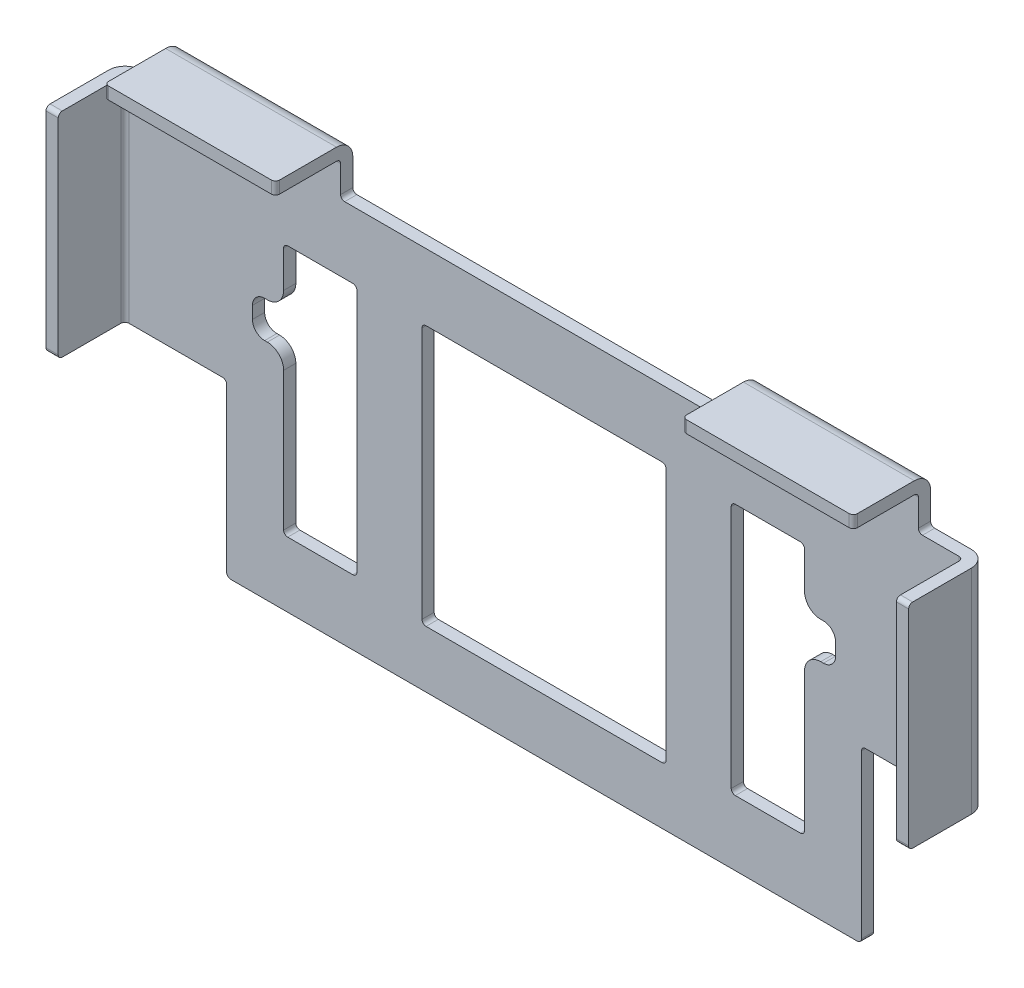
SolidWorks part; units mm, degrees
ref_plane "Front Plane" through (0, 0, 0) normal (0, 0, 1) x (1, 0, 0)
ref_plane "Top Plane" through (0, 0, 0) normal (0, 1, 0) x (1, 0, 0)
ref_plane "Right Plane" through (0, 0, 0) normal (1, 0, 0) x (0, 0, -1)
ref_plane "Plane1" through (0, 0, -42.5) normal (0, 0, -1) x (-1, 0, 0)
sketch "Sketch1" plane through (0, 0, -42.5) normal (0, 0, -1) x (-1, 0, 0)
  line L0 (53, 10.2) -> (-53, 10.2)
  line L1 (-53, 10.2) -> (-53, -16)
  line L2 (-53, -16) -> (53, -16)
  line L3 (53, -16) -> (53, 10.2)
extrude "Boss-Extrude1" add sketch "Sketch1" against normal blind 9.7
sketch "Sketch2" plane through (0, 10.2, 0) normal (0, 1, 0) x (-1, 0, 0)
  line L0 (51.5, -32.8) -> (-51.5, -32.8)
  line L1 (-51.5, -32.8) -> (-51.5, -41)
  line L2 (-51.5, -41) -> (51.5, -41)
  line L3 (51.5, -41) -> (51.5, -32.8)
extrude "Cut-Extrude1" cut sketch "Sketch2" against normal through all
sketch "Sketch3" plane through (0, 10.2, 0) normal (0, 1, 0) x (-1, 0, 0)
  line L0 (46, -41) -> (46, -42.5)
  line L1 (46, -42.5) -> (25, -42.5)
  line L2 (25, -42.5) -> (25, -41)
  line L3 (25, -41) -> (46, -41)
extrude "Boss-Extrude2" add sketch "Sketch3" along normal blind 5.8
sketch "Sketch4" plane through (0, 0, -41) normal (0, 0, 1) x (1, 0, 0)
  line L0 (-25, 16) -> (-25, 14.5)
  line L1 (-25, 14.5) -> (-46, 14.5)
  line L2 (-46, 14.5) -> (-46, 16)
  line L3 (-46, 16) -> (-25, 16)
extrude "Boss-Extrude3" add sketch "Sketch4" along normal blind 8
sketch "Sketch5" plane through (0, 10.2, 0) normal (0, 1, 0) x (-1, 0, 0)
  line L0 (-25, -41) -> (-25, -42.5)
  line L1 (-25, -42.5) -> (-46, -42.5)
  line L2 (-46, -42.5) -> (-46, -41)
  line L3 (-46, -41) -> (-25, -41)
extrude "Boss-Extrude4" add sketch "Sketch5" along normal blind 5.8
sketch "Sketch6" plane through (0, 0, -41) normal (0, 0, 1) x (1, 0, 0)
  line L0 (25, 14.5) -> (25, 16)
  line L1 (25, 16) -> (46, 16)
  line L2 (46, 16) -> (46, 14.5)
  line L3 (46, 14.5) -> (25, 14.5)
extrude "Boss-Extrude5" add sketch "Sketch6" along normal blind 8
sketch "Sketch7" plane through (0, -16, 0) normal (0, -1, 0) x (1, 0, 0)
  line L0 (-39, -41) -> (39, -41)
  line L1 (39, -41) -> (39, -42.5)
  line L2 (39, -42.5) -> (-39, -42.5)
  line L3 (-39, -42.5) -> (-39, -41)
extrude "Boss-Extrude6" add sketch "Sketch7" along normal blind 21
fillet "Fillet1" radius 0.5 4 edges at (-35.5, 14.5, -41) (35.5, 14.5, -41) (-51.5, -2.9, -41) (51.5, -2.9, -41)
fillet "Fillet2" radius 2 4 edges at (-53, -2.9, -42.5) (53, -2.9, -42.5) (-35.5, 16, -42.5) (35.5, 16, -42.5)
sketch "Sketch8" plane through (0, 0, -42.5) normal (0, 0, -1) x (-1, 0, 0)
  line L0 (0, 10.2) -> (0, -37) construction
  line L1 (25, 10.2) -> (-25, 10.2) construction
  line L2 (39, -37) -> (-39, -37) construction
  line L3 (15, 2) -> (-15, 2)
  line L4 (-15, 2) -> (-15, -30)
  line L5 (-15, -30) -> (15, -30)
  line L6 (-23, 2) -> (-32, 2)
  line L7 (-32, 2) -> (-32, -5)
  line L8 (-32, -5) -> (-35.8314, -5)
  line L9 (-35.8314, -5) -> (-35.8314, -9.5)
  line L10 (-35.8314, -9.5) -> (-32, -9.5)
  line L11 (-32, -9.5) -> (-32, -29)
  line L12 (-32, -29) -> (-23, -29)
  line L13 (-23, -29) -> (-23, 2)
  line L14 (32, -29) -> (23, -29)
  line L15 (32, -9.5) -> (32, -29)
  line L16 (35.8314, -9.5) -> (32, -9.5)
  line L17 (35.8314, -5) -> (35.8314, -9.5)
  line L18 (32, -5) -> (35.8314, -5)
  line L19 (32, 2) -> (32, -5)
  line L20 (23, 2) -> (32, 2)
  line L21 (23, -29) -> (23, 2)
  line L22 (15, 2) -> (15, -30)
  point P27 (0, -30)
  point P28 (0, 2)
  dimension "D1" = 32
  dimension "D2" = 15
  dimension "D3" = 7
  dimension "D4" = 8
  dimension "D5" = 9
  dimension "D6" = 4.5
  dimension "D7" = 7
  dimension "D8" = 31
extrude "Cut-Extrude2" cut sketch "Sketch8" against normal blind 1.5
fillet "Fillet4" radius 2 4 edges at (-32, -9.5, -41.75) (-32, -5, -41.75) (32, -9.5, -41.75) (32, -5, -41.75)
fillet "Fillet5" radius 1.5 4 edges at (-35.8314, -9.5, -41.75) (-35.8314, -5, -41.75) (35.8314, -5, -41.75) (35.8314, -9.5, -41.75)
fillet "Fillet6" radius 0.5 12 edges at (-15, 2, -41.75) (-15, -30, -41.75) (15, 2, -41.75) (-32, -29, -41.75) (-23, -29, -41.75) (-23, 2, -41.75) (-32, 2, -41.75) (32, 2, -41.75) (23, 2, -41.75) (23, -29, -41.75) (32, -29, -41.75) (15, -30, -41.75)
fillet "Fillet7" radius 0.5 16 edges at (39, -16, -41.75) (52.25, -16, -32.8) (52.25, 10.2, -32.8) (46, 10.2, -41.75) (46, 15.25, -33) (25, 15.25, -33) (25, 10.2, -41.75) (-25, 10.2, -41.75) (-25, 15.25, -33) (-46, 15.25, -33) (-46, 10.2, -41.75) (-52.25, 10.2, -32.8) (-52.25, -16, -32.8) (-39, -16, -41.75) (-39, -37, -41.75) (39, -37, -41.75)
